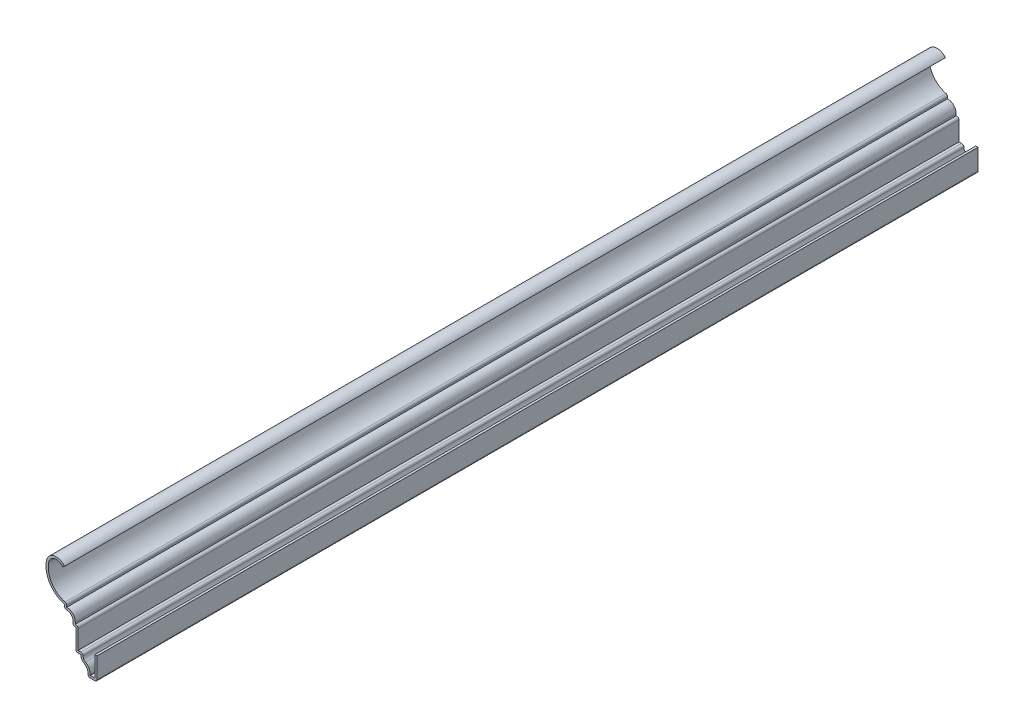
SolidWorks part; units mm, degrees
ref_plane "Front Plane" through (0, 0, 0) normal (0, 0, 1) x (1, 0, 0)
ref_plane "Top Plane" through (0, 0, 0) normal (0, 1, 0) x (1, 0, 0)
ref_plane "Right Plane" through (0, 0, 0) normal (1, 0, 0) x (0, 0, -1)
sketch "Sketch1" plane through (0, 0, 0) normal (0, 0, 1) x (1, 0, 0)
  line L0 (0, 0) -> (0, -12.7)
  line L1 (0, -12.7) -> (-5.1594, -12.7)
  line L2 (-9.1281, -3.9688) -> (-11.9062, -3.9688)
  line L3 (-11.9062, -3.9688) -> (-11.9063, 7.9375)
  line L4 (-11.9063, 7.9375) -> (-13.4938, 7.9375)
  line L5 (-18.2563, 13.4937) -> (-18.2563, 15.875)
  line L6 (-18.2562, 34.1888) -> (-9.5851, 22.1939) construction
  line L7 (-0.1933, -12.8282) -> (-0.1933, -0.1282) construction
  line L8 (-5.1594, -12.7) -> (-5.1594, -10.8428)
  line L9 (-13.4938, 7.9375) -> (-13.4938, 10.2403)
  arc A0 (-5.1594, -10.8428) -> (-7.1437, -7.4058) centre (-9.1281, -10.8428) ccw
  arc A1 (-7.1437, -7.4058) -> (-9.1281, -3.9688) centre (-5.1594, -3.9688) cw
  arc A2 (-13.4938, 10.2403) -> (-18.2563, 13.4937) centre (-16.9863, 10.2403) ccw
  arc A3 (-18.2563, 15.875) -> (-28.305, 32.0034) centre (-14.7079, 29.2804) cw
  arc A4 (-28.305, 32.0034) -> (-18.2562, 34.1888) centre (-22.8034, 30.9016) cw
  dimension "D14" = 12.7
  dimension "D7" = 11.1125
  dimension "D8" = 20.6375
  dimension "D13" = 10.3187
  dimension "D15" = 1.27
  dimension "D1" = 12.7
  dimension "D2" = 5.1594
  dimension "D3" = 3.9688
  dimension "D4" = 2.7781
  dimension "D5" = 1.5875
  dimension "D6" = 4.7625
  dimension "D9" = 8.7312
  dimension "D10" = 11.9062
  dimension "D11" = 5.5562
  dimension "D12" = 2.3813
extrude "Extrude-Thin1" add sketch "Sketch1" against normal blind 492.125 thin
fillet "Fillet1" radius 1.27 8 edges at (0, -12.7, -246.0625) (-11.9062, -3.9688, -246.0625) (-10.6363, 9.2075, -246.0625) (-5.1594, -12.7, -246.0625) (-7.5406, -2.6988, -246.0625) (-13.4938, 7.9375, -246.0625) (-18.2563, 13.4937, -246.0625) (-16.9863, 16.8911, -246.0625)
